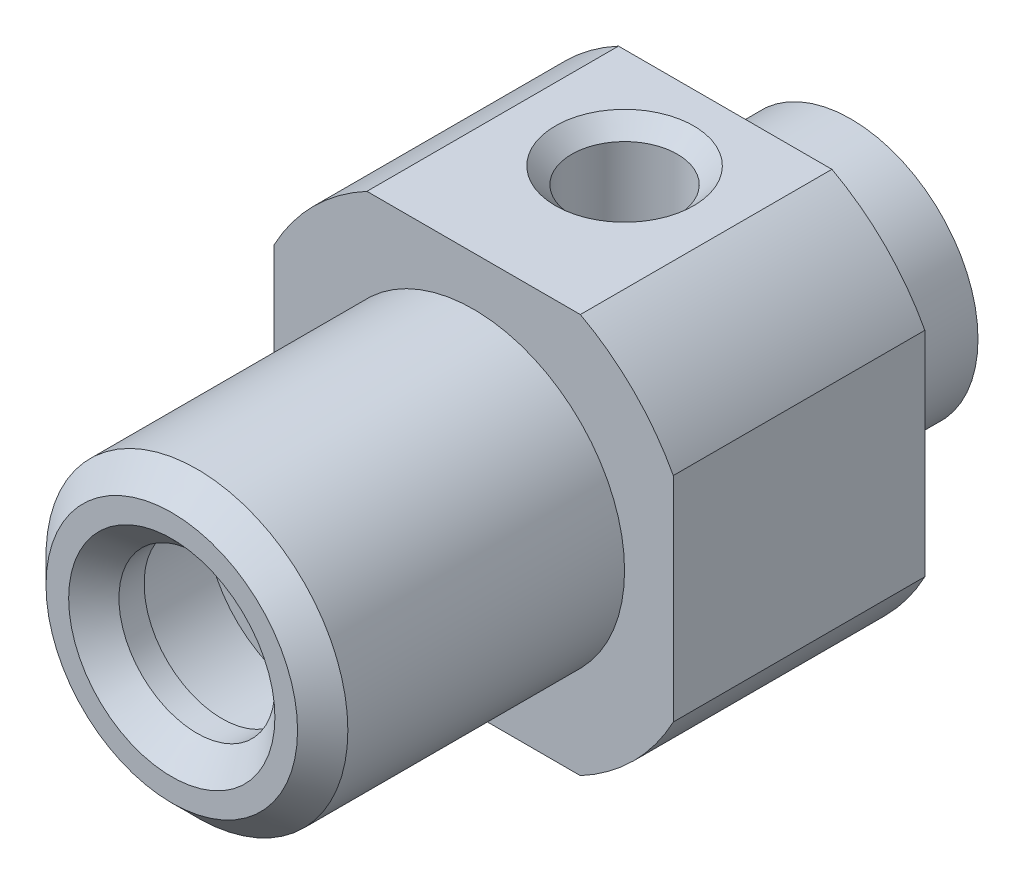
SolidWorks part; units mm, degrees
ref_plane "Front Plane" through (0, 0, 0) normal (0, 0, 1) x (1, 0, 0)
ref_plane "Top Plane" through (0, 0, 0) normal (0, 1, 0) x (1, 0, 0)
ref_plane "Right Plane" through (0, 0, 0) normal (1, 0, 0) x (0, 0, -1)
sketch "Sketch1" plane through (0, 0, 0) normal (1, 0, 0) x (0, 0, -1)
  line L0 (0, 0) -> (0, 5390.1232) construction
  line L1 (0, 0) -> (5390.1232, 0) construction
  line L2 (-12.5, 3.1) -> (-13.5, 4.1)
  line L3 (-13.5, 4.1) -> (-13.5, 5)
  line L4 (-13.5, 5) -> (-12.5, 6)
  line L5 (-12.5, 6) -> (-1.5, 6)
  line L6 (-1.5, 6) -> (-1.5, 9)
  line L7 (-1.5, 9) -> (8.5, 9)
  line L8 (8.5, 9) -> (8.5, 5.75)
  line L9 (8.5, 5.75) -> (9.85, 5.75)
  line L10 (9.85, 5.75) -> (9.85, 5.05)
  line L11 (9.85, 5.05) -> (13.5, 5.05)
  line L12 (13.5, 5.05) -> (13.5, 2.25)
  line L13 (13.5, 2.25) -> (-8, 2.25)
  line L14 (-11.5, 3.1) -> (-11.5, 4.15)
  line L15 (-11.5, 4.15) -> (-8, 4.15)
  line L16 (-8, 4.15) -> (-8, 2.25)
  line L17 (-11.5, 3.1) -> (-12.5, 3.1)
  dimension "D1" = 12
  dimension "D2" = 6.2
  dimension "D3" = 8.3
  dimension "D4" = 18
  dimension "D5" = 11.5
  dimension "D6" = 10.1
  dimension "D7" = 1.35
  dimension "D8" = 5
  dimension "D9" = 10
  dimension "D10" = 4.5
  dimension "D11" = 12
  dimension "D12" = 1
  dimension "D13" = 45
  dimension "D14" = 1
  dimension "D15" = 45
  dimension "D16" = 3.5
  dimension "D17" = 5.5
revolve "Revolve1" add sketch "Sketch1" angle 360 about L1
cosmetic thread "Cosmetic Thread1" parameters "D2"=10.619
sketch "Sketch2" plane through (0, 0, -8.5) normal (0, 0, -1) x (-1, 0, 0)
  line L1 (-7.9375, 7.9375) -> (7.9375, 7.9375)
  line L2 (-7.9375, 7.9375) -> (-7.9375, -7.9375)
  line L3 (-7.9375, -7.9375) -> (7.9375, -7.9375)
  line L4 (7.9375, 7.9375) -> (7.9375, -7.9375)
  line L5 (-7.9375, 7.9375) -> (7.9375, -7.9375) construction
  line L6 (-7.9375, -7.9375) -> (7.9375, 7.9375) construction
  point P0 (0, 0)
  circle M5 centre (0, 0) radius 9
  dimension "D1" = 15.875
extrude "Cut-Extrude2" cut sketch "Sketch2" against normal up to next contours L1 M5 | L2 M5 | L3 M5 | L4 M5
hole_wizard "M5x0.8 Tapped Hole1" positions "Sketch3" profile "Sketch4" tap size "M5x0.8" standard "JIS"
sketch "Sketch3" plane through (0, 7.9375, 0) normal (0, 1, 0) x (1, 0, 0)
  line L0 (0, 4.5) -> (0, 0) construction
  line L2 (4.2422, 8.5) -> (-4.2422, 8.5) construction
  point P0 (0, 4.5)
  dimension "D1" = 4
sketch "Sketch4" plane through (0, 7.9375, -4.5) normal (1, 0, 0) x (0, 0, 1)
  line L0 (0, 0) -> (0, 7)
  line L1 (0, 7) -> (2.1, 7)
  line L2 (2.1, 7) -> (2.1, 0.65)
  line L3 (2.1, 0.65) -> (2.75, 0)
  line L5 (2.75, 0) -> (0, 0)
  line L6 (-2.1, 0.65) -> (-2.75, 0) construction
  line L10 (0, 7) -> (-2.1, 7) construction
  line L11 (0, -6.35) -> (0, 107.95) construction
  dimension "Tap Drill Dia." = 4.2
  dimension "Tap Drill Depth" = 7
  dimension "Near C'Sink Dia." = 5.5
  dimension "Near C'Sink Angle" = 90
  dimension "Drill Angle" = 180
cosmetic thread "Hole Thread2" parameters "D1"=6, "D2"=5
ref_plane "Plane1" [suppressed] through (0, 15.5, 0) normal (0, 1, 0) x (1, 0, 0)
sketch "Sketch5" [suppressed] plane through (0, 15.5, 0) normal (0, 1, 0) x (1, 0, 0)
  line L0 (0, 0) -> (0, 50000) construction
  line L1 (0, 0) -> (50000, 0) construction
  line L2 (13.5, 14.75) -> (-13.5, 14.75) construction
  line L3 (-7.75, 14.75) -> (7.75, 14.75)
  line L4 (-7.75, 14.75) -> (-7.75, -0.75)
  line L5 (-7.75, -0.75) -> (7.75, -0.75)
  line L6 (7.75, 14.75) -> (7.75, -0.75)
  line L7 (-13.5, -0.75) -> (13.5, -0.75) construction
  dimension "D1" = 16.7946
extrude "Boss-Extrude1" [suppressed] add sketch "Sketch5" against normal up to surface (4.4462 mm away)
sketch "Sketch6" [suppressed] plane through (0, 0, 0) normal (1, 0, 0) x (0, 0, -1)
  line L0 (-19.9481, 0) -> (3.2487, 0) construction
  line L1 (-0.75, 10) -> (-2.25, 10)
  line L2 (-0.75, 11) -> (-0.75, -11) construction
  line L3 (-2.25, 10) -> (-5.7898, 13.5398)
  line L4 (-5.7898, 13.5398) -> (-0.75, 13.5398)
  line L5 (-0.75, 11.0538) -> (-0.75, -13.5) construction
  line L6 (-0.75, 13.5398) -> (-0.75, 10)
  dimension "D1" = 13.2321
  dimension "D2" = 1.0568
  dimension "D3" = 40.601
revolve "Cut-Revolve1" [suppressed] cut sketch "Sketch6" angle 360 about L0
hole_wizard "M5x0.8 Tapped Hole2" [suppressed] positions "Sketch7" profile "Sketch8" tap size "M5x0.8" standard "JIS"
sketch "Sketch7" plane through (0, 15.5, 0) normal (0, 1, 0) x (1, 0, 0)
  line L0 (0, 0) -> (0, 6.25) construction
  line L2 (10.6, 15.1) -> (-10.6, 15.1) construction
  point P0 (0, 6.25)
  dimension "D1" = 6.0393
sketch "Sketch8" plane through (0, 15.5, -6.25) normal (1, 0, 0) x (0, 0, 1)
  line L0 (0, 0) -> (0, 8)
  line L1 (0, 8) -> (2.1, 8)
  line L2 (2.1, 8) -> (2.1, 0.425)
  line L3 (2.1, 0.425) -> (2.525, 0)
  line L5 (2.525, 0) -> (0, 0)
  line L6 (-2.1, 0.425) -> (-2.525, 0) construction
  line L10 (0, 8) -> (-2.1, 8) construction
  line L11 (0, -6.35) -> (0, 107.95) construction
  dimension "Tap Drill Dia." = 4.2
  dimension "Tap Drill Depth" = 8
  dimension "Near C'Sink Dia." = 5.05
  dimension "Near C'Sink Angle" = 90
  dimension "Drill Angle" = 180
cosmetic thread "Hole Thread3" [suppressed] parameters "D1"=6.5, "D2"=5
hole_wizard "G1/8 Tapped Hole1" [suppressed] positions "Sketch9" profile "Sketch10" tap size "G1/8" standard "JIS"
sketch "Sketch9" plane through (0, 15.5, 0) normal (0, 1, 0) x (1, 0, 0)
  line L0 (13.1, 16.1) -> (-13.1, 16.1) construction
  line L1 (0, 6.8) -> (0, 0) construction
  point P0 (0, 6.8)
  dimension "D1" = 9.0659
sketch "Sketch10" plane through (0, 15.5, -6.8) normal (1, 0, 0) x (0, 0, 1)
  line L0 (0, 0) -> (0, 10)
  line L1 (0, 10) -> (4.4, 10)
  line L2 (4.4, 10) -> (4.4, 0.489)
  line L3 (4.4, 0.489) -> (4.889, 0)
  line L5 (4.889, 0) -> (0, 0)
  line L6 (-4.4, 0.489) -> (-4.889, 0) construction
  line L10 (0, 10) -> (-4.4, 10) construction
  line L11 (0, -6.35) -> (0, 107.95) construction
  dimension "Tap Drill Dia." = 8.8
  dimension "Tap Drill Depth" = 10
  dimension "Near C'Sink Dia." = 9.778
  dimension "Near C'Sink Angle" = 90
  dimension "Drill Angle" = 180
cosmetic thread "Hole Thread4" [suppressed] parameters "D1"=8, "D2"=9.728
